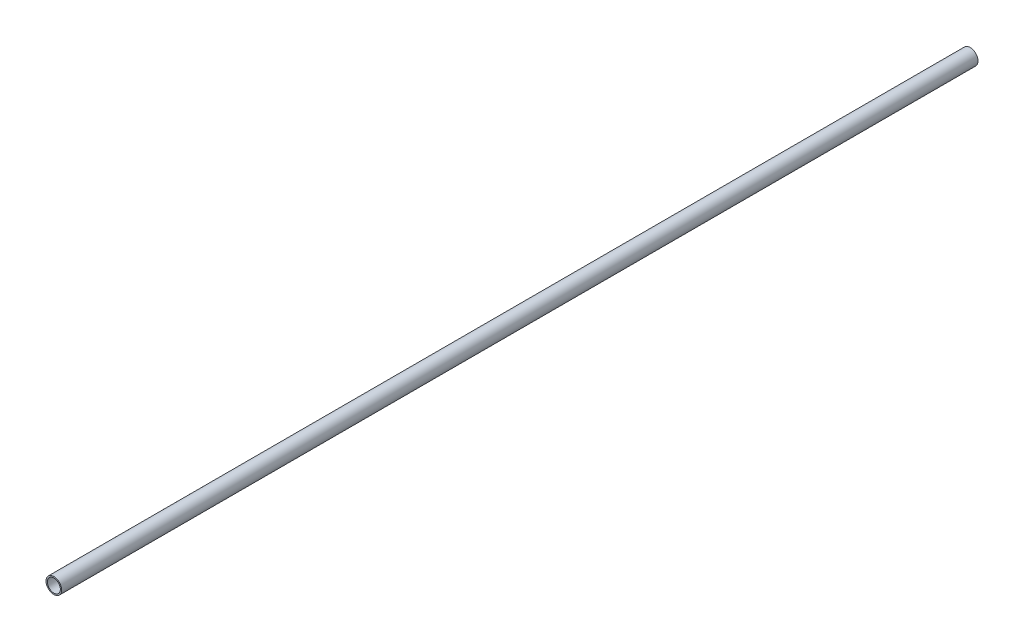
SolidWorks part; units mm, degrees
ref_plane "Front Plane" through (0, 0, 0) normal (0, 0, 1) x (1, 0, 0)
ref_plane "Top Plane" through (0, 0, 0) normal (0, 1, 0) x (1, 0, 0)
ref_plane "Right Plane" through (0, 0, 0) normal (1, 0, 0) x (0, 0, -1)
sketch "Sketch1" plane through (0, 0, 0) normal (0, 0, 1) x (1, 0, 0)
  circle A0 centre (0, 0) radius 21.082
  circle A1 centre (0, 0) radius 17.526
  dimension "D1" = 42.164
  dimension "D2" = 35.052
extrude "Boss-Extrude1" add sketch "Sketch1" along normal blind 2463.8
